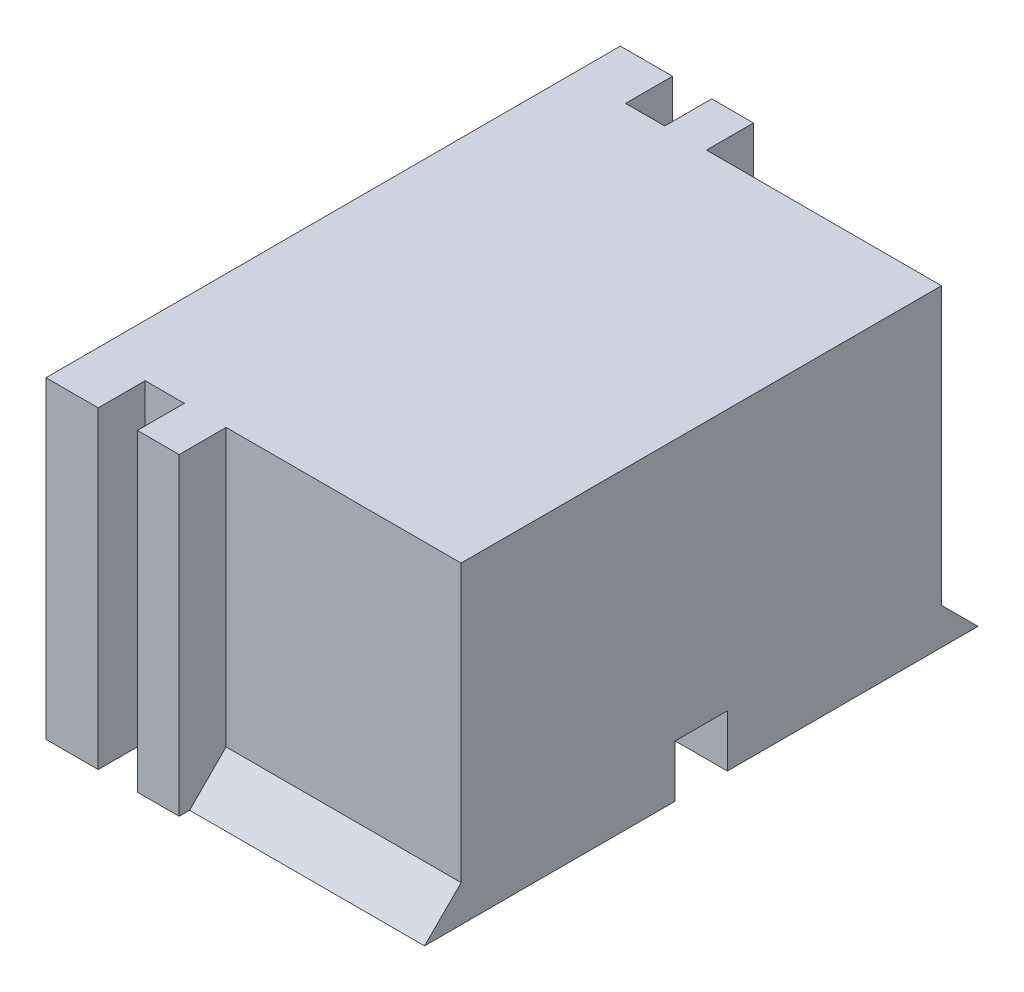
SolidWorks part; units mm, degrees
ref_plane "Спереди" through (0, 0, 0) normal (0, 0, 1) x (1, 0, 0)
ref_plane "Сверху" through (0, 0, 0) normal (0, 1, 0) x (1, 0, 0)
ref_plane "Справа" through (0, 0, 0) normal (1, 0, 0) x (0, 0, -1)
sketch "Эскиз1" plane through (0, 0, 0) normal (0, 0, 1) x (1, 0, 0)
  line L1 (-2.0873, 6.7397) -> (12.0127, 6.7397)
  line L2 (-2.0873, 6.7397) -> (-2.0873, -5.2603)
  line L3 (-2.0873, -5.2603) -> (12.0127, -5.2603)
  line L4 (12.0127, 6.7397) -> (12.0127, -5.2603)
  dimension "D1" = 14.1
  dimension "D2" = 12
extrude "Бобышка-Вытянуть1" add sketch "Эскиз1" along normal blind 11
sketch "Эскиз2" plane through (0, 0, 0) normal (0, 0, -1) x (-1, 0, 0)
  line L0 (-12.0127, 6.7397) -> (2.0873, 6.7397) construction
  line L1 (-1.4127, 6.7397) -> (0.0873, 6.7397)
  line L2 (-1.4127, 6.7397) -> (-1.4127, -5.2603)
  line L3 (-1.4127, -5.2603) -> (0.0873, -5.2603)
  line L4 (0.0873, 6.7397) -> (0.0873, -5.2603)
  line L5 (2.0873, -5.2603) -> (-12.0127, -5.2603) construction
  line L6 (2.0873, 6.7397) -> (2.0873, -5.2603) construction
  dimension "D1" = 0
  dimension "D2" = 0
  dimension "D3" = 2
  dimension "D4" = 1.5
extrude "Вырез-Вытянуть1" cut sketch "Эскиз2" against normal blind 1.8
sketch "Эскиз3" plane through (0, 0, 0) normal (0, 0, -1) x (-1, 0, 0)
  line L0 (-12.0127, 6.7397) -> (-1.4127, 6.7397) construction
  line L1 (-12.0127, 6.7397) -> (-3.0127, 6.7397)
  line L2 (-12.0127, 6.7397) -> (-12.0127, -5.2603)
  line L3 (-12.0127, -5.2603) -> (-3.0127, -5.2603)
  line L4 (-3.0127, 6.7397) -> (-3.0127, -5.2603)
  line L5 (-1.4127, -5.2603) -> (-12.0127, -5.2603) construction
  line L6 (-12.0127, -5.2603) -> (-12.0127, 6.7397) construction
  dimension "D1" = 0
  dimension "D2" = 0
  dimension "D3" = 0
  dimension "D4" = 9
extrude "Вырез-Вытянуть2" cut sketch "Эскиз3" against normal blind 1.8
sketch "Эскиз4" plane through (12.0127, 0, 0) normal (1, 0, 0) x (0, 0, -1)
  line L0 (-1.8, -5.2603) -> (-0.4, -5.2603)
  line L1 (-0.4, -5.2603) -> (-1.8, -3.8603)
  line L2 (-1.8, 6.7397) -> (-1.8, -5.2603) construction
  line L3 (-1.8, -3.8603) -> (-1.8, -5.2603)
  dimension "D1" = 1.4
  dimension "D2" = 1.4
extrude "Бобышка-Вытянуть2" add sketch "Эскиз4" against normal blind 9
sketch "Эскиз5" plane through (12.0127, 0, 0) normal (1, 0, 0) x (0, 0, -1)
  line L0 (-11, -5.2603) -> (-0.4, -5.2603) construction
  line L1 (-11, -3.2603) -> (-10, -3.2603)
  line L2 (-11, -3.2603) -> (-11, -5.2603)
  line L3 (-11, -5.2603) -> (-10, -5.2603)
  line L4 (-10, -3.2603) -> (-10, -5.2603)
  line L5 (-11, -5.2603) -> (-11, 6.7397) construction
  dimension "D1" = 2
  dimension "D2" = 1
  dimension "D3" = 0
  dimension "D4" = 0
extrude "Вырез-Вытянуть3" cut sketch "Эскиз5" against normal blind 12
mirror "Зеркальное отражение1" about plane through (0, 0, 11) normal (0, 0, 1) of "Бобышка-Вытянуть1", "Вырез-Вытянуть1", "Вырез-Вытянуть2", "Бобышка-Вытянуть2", "Вырез-Вытянуть3"
